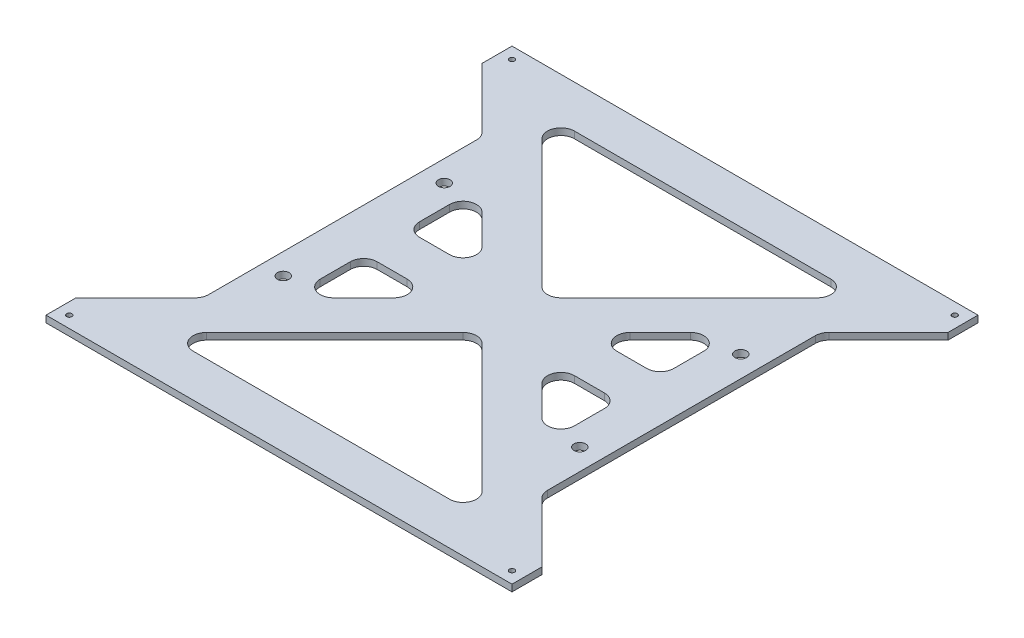
SolidWorks part; units mm, degrees
material "6061-T6 (SS)"
ref_plane "Front Plane" through (0, 0, 0) normal (0, 0, 1) x (1, 0, 0)
ref_plane "Top Plane" through (0, 0, 0) normal (0, 1, 0) x (1, 0, 0)
ref_plane "Right Plane" through (0, 0, 0) normal (1, 0, 0) x (0, 0, -1)
sketch "Sketch1" plane through (0, 0, 0) normal (0, 1, 0) x (1, 0, 0)
  line L0 (-110, 110) -> (110, -110) construction
  line L1 (-110, 110) -> (110, 110)
  line L2 (-110, 110) -> (-110, -110)
  line L3 (-110, -110) -> (110, -110)
  line L4 (110, 110) -> (110, -110)
  point P10 (110, 110)
  point P16 (-110, -110)
  dimension "D1" = 220
  dimension "D2" = 220
extrude "Boss-Extrude1" add sketch "Sketch1" along normal blind 3.175
hole_wizard "M3x0.5 Tapped Hole1" positions "Sketch3" profile "Sketch2" tap size "M3x0.5" standard "Ansi Metric" end condition through all
sketch "Sketch3" plane through (0, 3.175, 0) normal (0, 1, 0) x (-1, 0, 0)
  line L0 (-104.5, 104.5) -> (104.5, -104.5) construction
  point P0 (104.5, -104.5)
  point P1 (-104.5, -104.5)
  point P3 (-104.5, 104.5)
  point P5 (104.5, 104.5)
  dimension "D1" = 209
  dimension "D2" = 209
sketch "Sketch2" plane through (-104.5, 3.175, -104.5) normal (1, 0, 0) x (0, 0, 1)
  line L0 (0, 0) -> (0, 3.175)
  line L1 (0, 3.175) -> (1.25, 3.175)
  line L2 (1.25, 3.175) -> (1.25, 0)
  line L5 (1.25, 0) -> (0, 0)
  line L11 (0, -6.35) -> (0, 107.95) construction
  dimension "Thru Tap Drill Dia." = 2.5
  dimension "Thru Tap Drill Depth" = 3.175
cosmetic thread "Hole Thread1" parameters "D2"=3
cosmetic thread "Hole Thread2" parameters "D2"=3
cosmetic thread "Hole Thread3" parameters "D2"=3
cosmetic thread "Hole Thread4" parameters "D2"=3
sketch "Sketch4" plane through (0, 3.175, 0) normal (0, 1, 0) x (1, 0, 0)
  line L0 (70, 38) -> (-70, -38) construction
  circle A0 centre (-70, 38) radius 2.75
  circle A1 centre (-70, -38) radius 2.75
  circle A2 centre (70, -38) radius 2.75
  circle A3 centre (70, 38) radius 2.75
  dimension "D1" = 5.5
  dimension "D2" = 140
  dimension "D3" = 76
extrude "Cut-Extrude1" cut sketch "Sketch4" against normal through all
sketch "Sketch5" plane through (0, 3.175, 0) normal (0, 1, 0) x (1, 0, 0)
  line L0 (-110, 110) -> (110, -110) construction
  line L1 (-110, -110) -> (110, 110) construction
  line L2 (-110, 0) -> (110, 0) construction
  line L3 (-110, 110) -> (-110, -110) construction
  line L4 (110, -110) -> (110, 110) construction
  line L5 (-65.0177, 79.1599) -> (-4.4901, 18.6323)
  line L6 (4.4901, 18.6323) -> (65.0177, 79.1599)
  line L7 (60.5276, 90) -> (-60.5276, 90)
  line L8 (-4.4901, -18.6323) -> (-65.0177, -79.1599)
  line L9 (-60.5276, -90) -> (60.5276, -90)
  line L10 (65.0177, -79.1599) -> (4.4901, -18.6323)
  line L11 (-60, -16.35) -> (-60, -30.5276)
  line L12 (-49.1599, -35.0177) -> (-34.9823, -20.8401)
  line L13 (-39.4724, -10) -> (-53.65, -10)
  line L14 (39.4724, -10) -> (53.65, -10)
  line L15 (60, -16.35) -> (60, -30.5276)
  line L16 (49.1599, -35.0177) -> (34.9823, -20.8401)
  line L17 (34.9823, 20.8401) -> (49.1599, 35.0177)
  line L18 (60, 30.5276) -> (60, 16.35)
  line L19 (53.65, 10) -> (39.4724, 10)
  line L20 (-39.4724, 10) -> (-53.65, 10)
  line L21 (-60, 16.35) -> (-60, 30.5276)
  line L22 (-49.1599, 35.0177) -> (-34.9823, 20.8401)
  line L23 (-110, -110) -> (110, -110) construction
  line L24 (110, 110) -> (-110, 110) construction
  line L25 (-110, 95.8579) -> (-110, -95.8579)
  line L26 (-110, -95.8579) -> (-81.8599, -67.7177)
  line L27 (-80, -63.2276) -> (-80, 63.2276)
  line L28 (-81.8599, 67.7177) -> (-110, 95.8579)
  line L29 (110, 95.8579) -> (81.8599, 67.7177)
  line L30 (80, 63.2276) -> (80, -63.2276)
  line L31 (81.8599, -67.7177) -> (110, -95.8579)
  line L32 (110, -95.8579) -> (110, 95.8579)
  circle A0 centre (-70, -38) radius 2.75 construction
  circle A1 centre (70, -38) radius 2.75 construction
  arc A2 (-65.0177, 79.1599) -> (-60.5276, 90) centre (-60.5276, 83.65) cw
  arc A3 (65.0177, 79.1599) -> (60.5276, 90) centre (60.5276, 83.65) ccw
  arc A4 (-4.4901, 18.6323) -> (4.4901, 18.6323) centre (0, 23.1224) ccw
  arc A5 (-4.4901, -18.6323) -> (4.4901, -18.6323) centre (0, -23.1224) cw
  arc A6 (60.5276, -90) -> (65.0177, -79.1599) centre (60.5276, -83.65) ccw
  arc A7 (-65.0177, -79.1599) -> (-60.5276, -90) centre (-60.5276, -83.65) ccw
  arc A8 (60, -30.5276) -> (49.1599, -35.0177) centre (53.65, -30.5276) cw
  arc A9 (39.4724, -10) -> (34.9823, -20.8401) centre (39.4724, -16.35) ccw
  arc A10 (53.65, -10) -> (60, -16.35) centre (53.65, -16.35) cw
  arc A11 (60, 16.35) -> (53.65, 10) centre (53.65, 16.35) cw
  arc A12 (49.1599, 35.0177) -> (60, 30.5276) centre (53.65, 30.5276) cw
  arc A13 (34.9823, 20.8401) -> (39.4724, 10) centre (39.4724, 16.35) ccw
  arc A14 (-39.4724, 10) -> (-34.9823, 20.8401) centre (-39.4724, 16.35) ccw
  arc A15 (-60, 30.5276) -> (-49.1599, 35.0177) centre (-53.65, 30.5276) cw
  arc A16 (-53.65, 10) -> (-60, 16.35) centre (-53.65, 16.35) cw
  arc A17 (-60, -16.35) -> (-53.65, -10) centre (-53.65, -16.35) cw
  arc A18 (-34.9823, -20.8401) -> (-39.4724, -10) centre (-39.4724, -16.35) ccw
  arc A19 (-60, -30.5276) -> (-49.1599, -35.0177) centre (-53.65, -30.5276) ccw
  arc A20 (81.8599, 67.7177) -> (80, 63.2276) centre (86.35, 63.2276) ccw
  arc A21 (80, -63.2276) -> (81.8599, -67.7177) centre (86.35, -63.2276) ccw
  arc A22 (-81.8599, -67.7177) -> (-80, -63.2276) centre (-86.35, -63.2276) ccw
  arc A23 (-80, 63.2276) -> (-81.8599, 67.7177) centre (-86.35, 63.2276) ccw
  point P75 (-24.1421, -10)
  dimension "D11" = 6.35
  dimension "D12" = 6.35
  dimension "D15" = 6.35
  dimension "D1" = 10
  dimension "D2" = 20
  dimension "D3" = 20
  dimension "D4" = 20
  dimension "D5" = 10
  dimension "D6" = 20
  dimension "D7" = 20
  dimension "D8" = 20
  dimension "D9" = 10
  dimension "D10" = 10
  dimension "D13" = 20
  dimension "D14" = 20
extrude "Cut-Extrude2" cut sketch "Sketch5" against normal through all
